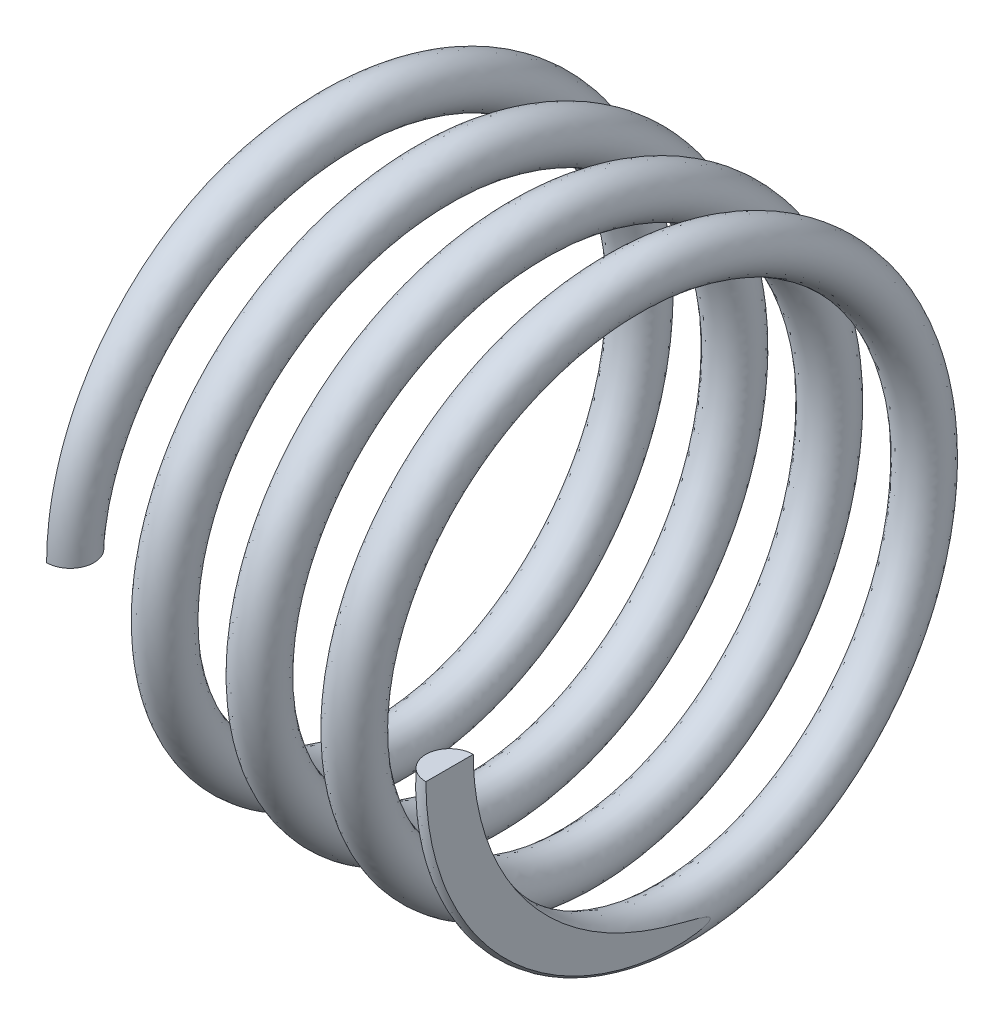
SolidWorks part; units mm, degrees
ref_plane "Спереди" through (0, 0, 0) normal (0, 0, 1) x (1, 0, 0)
ref_plane "Сверху" through (0, 0, 0) normal (0, 1, 0) x (1, 0, 0)
ref_plane "Справа" through (0, 0, 0) normal (1, 0, 0) x (0, 0, -1)
sketch "Эскиз2" plane through (0, 0, 0) normal (1, 0, 0) x (0, 0, -1)
  circle A0 centre (0, 0) radius 5.5
curve "Спираль1" pitch 2 height 8 turns 4
sketch "Эскиз3" plane through (0, 0, 0) normal (0, 1, 0) x (1, 0, 0)
  circle A0 centre (8.0017, -5.4991) radius 0.5
sweep "По траектории1" add profiles "Эскиз3" path "Спираль1"
sketch "Эскиз6" plane through (0, 0, 0) normal (0, 1, 0) x (1, 0, 0)
  line L1 (0.0017, -6.3636) -> (-2.2511, -6.3636)
  line L2 (0.0017, -6.3636) -> (0.0017, 0)
  line L3 (0.0017, 0) -> (-2.2511, 0)
  line L4 (-2.2511, -6.3636) -> (-2.2511, 0)
extrude "Вытянуть2" cut sketch "Эскиз6" along normal blind 10
sketch "Эскиз8" plane through (0, 0, 0) normal (0, 1, 0) x (1, 0, 0)
  line L1 (8.0017, -5.9991) -> (10.0599, -5.9991)
  line L2 (8.0017, -5.9991) -> (8.0017, 3.0518)
  line L3 (8.0017, 3.0518) -> (10.0599, 3.0518)
  line L4 (10.0599, -5.9991) -> (10.0599, 3.0518)
  circle A0 centre (8.0017, -5.4991) radius 0.5 construction
extrude "Вытянуть3" cut sketch "Эскиз8" against normal blind 10
sketch "Эскиз9" plane through (0, 0, 0) normal (1, 0, 0) x (0, 0, -1)
  circle A0 centre (0, 0) radius 8.7267
